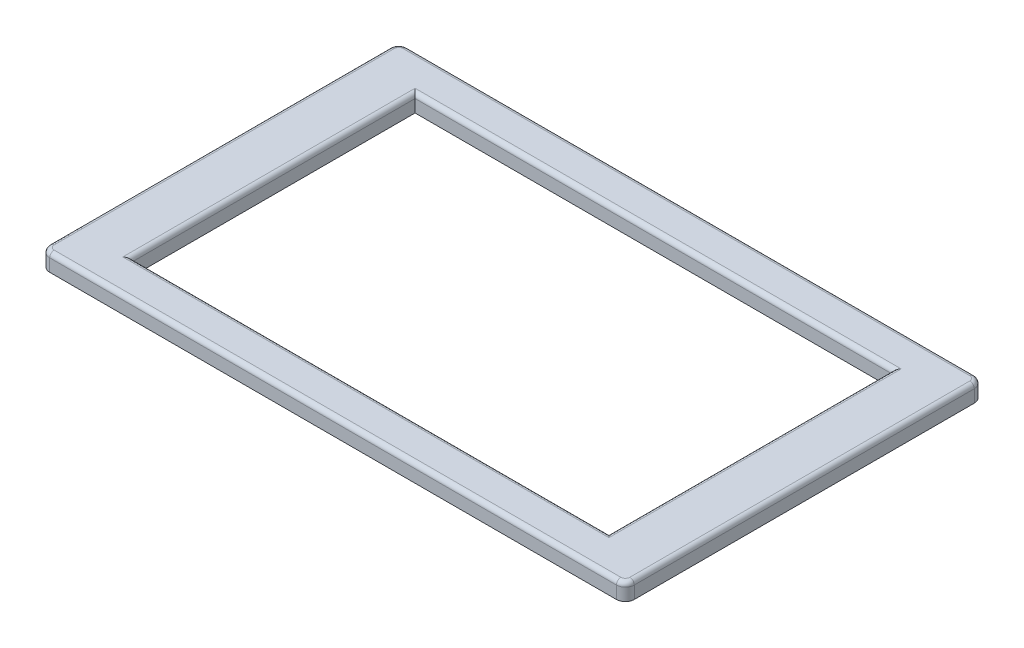
SolidWorks part; units mm, degrees
ref_plane "Alzado" through (0, 0, 0) normal (0, 0, 1) x (1, 0, 0)
ref_plane "Planta" through (0, 0, 0) normal (0, 1, 0) x (1, 0, 0)
ref_plane "Vista lateral" through (0, 0, 0) normal (1, 0, 0) x (0, 0, -1)
sketch "Croquis1" plane through (0, 0, 0) normal (0, 1, 0) x (1, 0, 0)
  line L0 (4, 120) -> (194, 120)
  line L1 (194, 0) -> (4, 0)
  line L6 (1, 3) -> (1, 117)
  line L9 (197, 3) -> (197, 117)
  line L15 (179, 107.5) -> (179, 12.5)
  line L16 (179, 12.5) -> (19, 12.5)
  line L17 (19, 12.5) -> (19, 107.5)
  line L18 (19, 107.5) -> (179, 107.5)
  arc A0 (1, 3) -> (4, 0) centre (4, 3) ccw
  arc A1 (1, 117) -> (4, 120) centre (4, 117) cw
  arc A2 (197, 117) -> (194, 120) centre (194, 117) ccw
  arc A8 (197, 3) -> (194, 0) centre (194, 3) cw
extrude "Saliente-Extruir3" add sketch "Croquis1" along normal blind 5.7
fillet "Redondeo2" radius 1.5 12 edges at (19, 5.7, -60) (99, 5.7, -12.5) (179, 5.7, -60) (99, 5.7, -107.5) (99, 5.7, -120) (196.1213, 5.7, -119.1213) (197, 5.7, -60) (196.1213, 5.7, -0.8787) (99, 5.7, 0) (1.8787, 5.7, -0.8787) (1, 5.7, -60) (1.8787, 5.7, -119.1213)
sketch "Croquis2" plane through (0, 0, 0) normal (0, -1, 0) x (1, 0, 0)
  circle A0 centre (5, -27.3877) radius 2
  circle A1 centre (5, -87.3877) radius 2
  circle A2 centre (193, -27.3877) radius 2
  circle A3 centre (193, -87.3877) radius 2
extrude "Cortar-Extruir1" cut sketch "Croquis2" against normal blind 3.1
